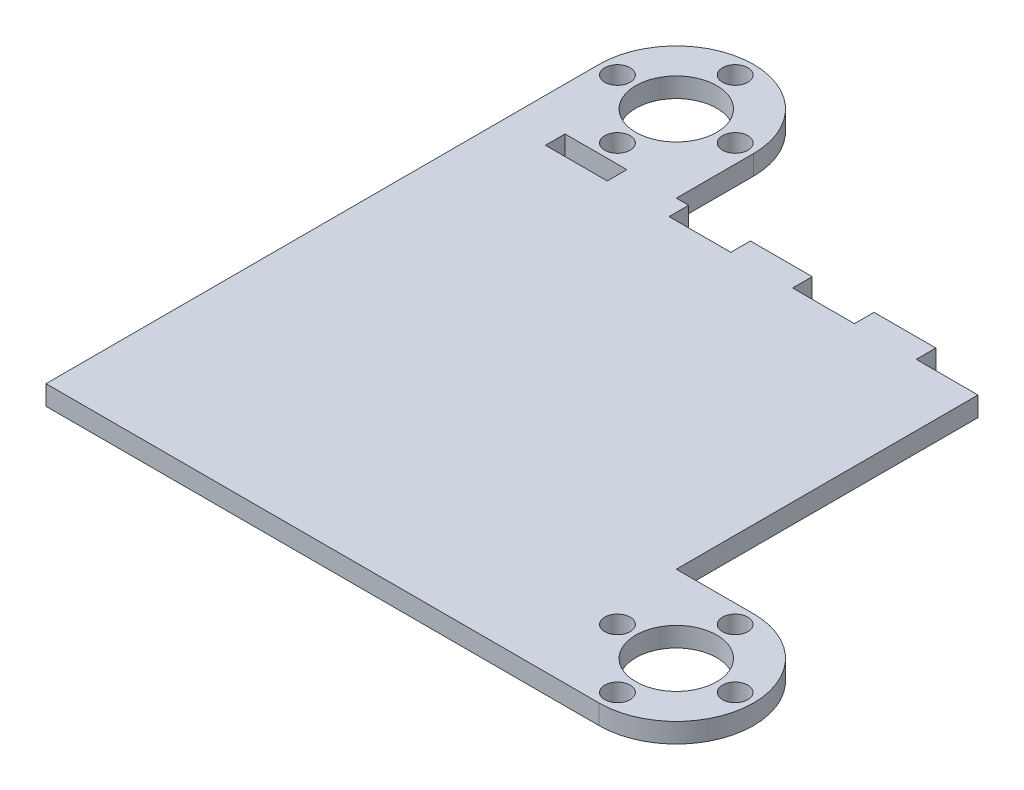
SolidWorks part; units mm, degrees
ref_plane "Front Plane" through (0, 0, 0) normal (0, 0, 1) x (1, 0, 0)
ref_plane "Top Plane" through (0, 0, 0) normal (0, 1, 0) x (1, 0, 0)
ref_plane "Right Plane" through (0, 0, 0) normal (1, 0, 0) x (0, 0, -1)
sketch "Sketch1" plane through (0, 0, 0) normal (0, 1, 0) x (1, 0, 0)
  line L0 (-38.5, 51) -> (-38.5, 38.5)
  line L1 (-13.5, 38.5) -> (38.5, 38.5)
  line L2 (-38.5, 38.5) -> (-38.5, -38.5)
  line L3 (-38.5, -38.5) -> (38.5, -38.5)
  line L4 (38.5, 38.5) -> (38.5, -13.5)
  line L5 (-13.5, 51) -> (-13.5, 38.5)
  line L6 (51, -13.5) -> (38.5, -13.5)
  line L7 (51, -38.5) -> (38.5, -38.5)
  line L8 (51, -19.45) -> (51, -13.5) construction
  line L9 (-26, 57.55) -> (-26, 63.5) construction
  line L10 (38.5, -26) -> (38.5, -38.5)
  arc A1 (-13.5, 51) -> (-38.5, 51) centre (-26, 51) ccw
  arc A2 (51, -38.5) -> (51, -13.5) centre (51, -26) ccw
  circle A3 centre (-26, 51) radius 6.55
  circle A4 centre (51, -26) radius 6.55
  circle A5 centre (-26, 51) radius 9.5 construction
  circle A6 centre (51, -26) radius 9.5 construction
  circle A7 centre (-26, 60.525) radius 2.05
  circle A11 centre (51, -16.475) radius 2.05
  circle A18 centre (-16.475, 51) radius 2.05
  circle A19 centre (-26, 41.475) radius 2.05
  circle A20 centre (-35.525, 51) radius 2.05
  circle A21 centre (137.525, 51) radius 2.05
  circle A22 centre (60.525, -26) radius 2.05
  circle A23 centre (128, -112.525) radius 2.05
  circle A24 centre (51, -35.525) radius 2.05
  circle A25 centre (-35.525, -103) radius 2.05
  circle A26 centre (41.475, -26) radius 2.05
  point P35 (-26, 51)
  point P48 (51, -26)
  dimension "D5" = 25
  dimension "D7" = 25
  dimension "D9" = 13.1
  dimension "D10" = 13.1
  dimension "D11" = 19
  dimension "D12" = 19
  dimension "D13" = 4.1
  dimension "D15" = 4.1
  dimension "D1" = 77
  dimension "D2" = 77
  dimension "D3" = 38.5
  dimension "D4" = 38.5
  dimension "D6" = 12.5
  dimension "D8" = 12.5
  dimension "D14" = 4
  dimension "D16" = 4
extrude "Boss-Extrude1" add sketch "Sketch1" along normal blind 3.175
sketch "Sketch2" plane through (0, 3.175, 0) normal (0, 1, 0) x (1, 0, 0)
  line L0 (-13.5, 38.5) -> (38.5, 38.5) construction
  line L1 (38.5, 38.5) -> (28.5, 38.5)
  line L2 (38.5, 38.5) -> (38.5, 35.325)
  line L3 (38.5, 35.325) -> (28.5, 35.325)
  line L4 (28.5, 38.5) -> (28.5, 35.325)
  line L5 (38.5, 38.5) -> (38.5, -13.5) construction
  line L6 (18.5, 38.5) -> (8.5, 38.5)
  line L7 (8.5, 38.5) -> (8.5, 35.325)
  line L8 (18.5, 35.325) -> (8.5, 35.325)
  line L9 (18.5, 38.5) -> (18.5, 35.325)
  line L10 (-1.5, 38.5) -> (-11.5, 38.5)
  line L11 (-11.5, 38.5) -> (-11.5, 35.325)
  line L12 (-1.5, 35.325) -> (-11.5, 35.325)
  line L13 (-1.5, 38.5) -> (-1.5, 35.325)
  line L14 (-21.5, 38.5) -> (-31.5, 38.5)
  line L15 (-31.5, 38.5) -> (-31.5, 35.325)
  line L16 (-21.5, 35.325) -> (-31.5, 35.325)
  line L17 (-21.5, 38.5) -> (-21.5, 35.325)
  dimension "D1" = 3.175
  dimension "D2" = 10
  dimension "D3" = 0
  dimension "D4" = 4
extrude "Cut-Extrude1" cut sketch "Sketch2" against normal blind 3.175
equation "\"elevator width\"=77"
equation "\"D1@Sketch1\"=\"elevator width\""
equation "\"D2@Sketch1\"=\"elevator width\""
equation "\"D3@Sketch1\"=\"elevator width\"/2"
equation "\"D4@Sketch1\"=\"elevator width\"/2"
equation "\"drivign screw diameter\"=25"
equation "\"D5@Sketch1\"=\"drivign screw diameter\""
equation "\"D6@Sketch1\"=\"drivign screw diameter\"/2"
equation "\"D7@Sketch1\"=\"drivign screw diameter\""
equation "\"D8@Sketch1\"=\"drivign screw diameter\"/2"
equation "\"lead screw diameter\"=13.1"
equation "\"D9@Sketch1\"=\"lead screw diameter\""
equation "\"D10@Sketch1\"=\"lead screw diameter\""
equation "\"lead screw hole diameter\"=19"
equation "\"D11@Sketch1\"=\"lead screw hole diameter\""
equation "\"D12@Sketch1\"=\"lead screw hole diameter\""
equation "\"lead screw mounting hole\"=4.1"
equation "\"D13@Sketch1\"=\"lead screw mounting hole\""
equation "\"D15@Sketch1\"=\"lead screw mounting hole\""
